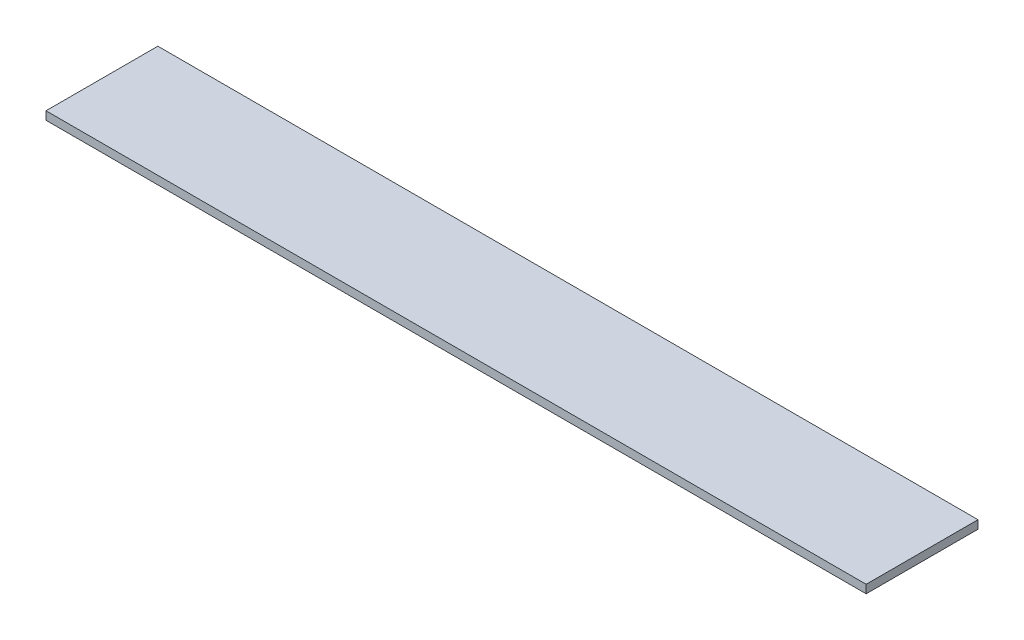
SolidWorks part; units mm, degrees
material "Acrylic (Medium-high impact)"
ref_plane "Front Plane" through (0, 0, 0) normal (0, 0, 1) x (1, 0, 0)
ref_plane "Top Plane" through (0, 0, 0) normal (0, 1, 0) x (1, 0, 0)
ref_plane "Right Plane" through (0, 0, 0) normal (1, 0, 0) x (0, 0, -1)
sketch "Sketch1" plane through (0, 0, 0) normal (0, 1, 0) x (1, 0, 0)
  line L0 (-185, -73.025) -> (373.7224, -73.025)
  line L1 (175, 3.175) -> (-175, 3.175)
  line L2 (-185, -6.825) -> (-185, 3.175)
  line L3 (357.3724, -3.175) -> (-168.65, -3.175) construction
  line L4 (-185, 3.175) -> (-175, 3.175)
  line L5 (175, 3.175) -> (373.7224, 3.175)
  line L6 (373.7224, 3.175) -> (373.7224, -6.825)
  line L8 (-185, -6.825) -> (-185, -73.025)
  line L9 (-185, -73.025) -> (-178.65, -73.025) construction
  line L10 (-178.65, -13.175) -> (-178.65, -73.025) construction
  line L12 (373.7224, -6.825) -> (373.7224, -73.025)
  line L13 (373.7224, -73.025) -> (367.3724, -73.025) construction
  line L14 (367.3724, -13.175) -> (367.3724, -73.025) construction
  arc A0 (357.3724, -3.175) -> (367.3724, -13.175) centre (357.3724, -13.175) cw construction
  arc A1 (-168.65, -3.175) -> (-178.65, -13.175) centre (-168.65, -13.175) ccw construction
  point P0 (0, 0)
  point P17 (373.7224, 3.175)
  point P20 (-185, 3.175)
  dimension "D10" = 10
  dimension "D2" = 558.7224
  dimension "D3" = 76.2
  dimension "D4" = 76.2
  dimension "D5" = 185
  dimension "D6" = 3.175
  dimension "D7" = 3.175
  dimension "D8" = 6.35
  dimension "D9" = 6.35
extrude "Boss-Extrude1" add sketch "Sketch1" along normal blind 5.6388
